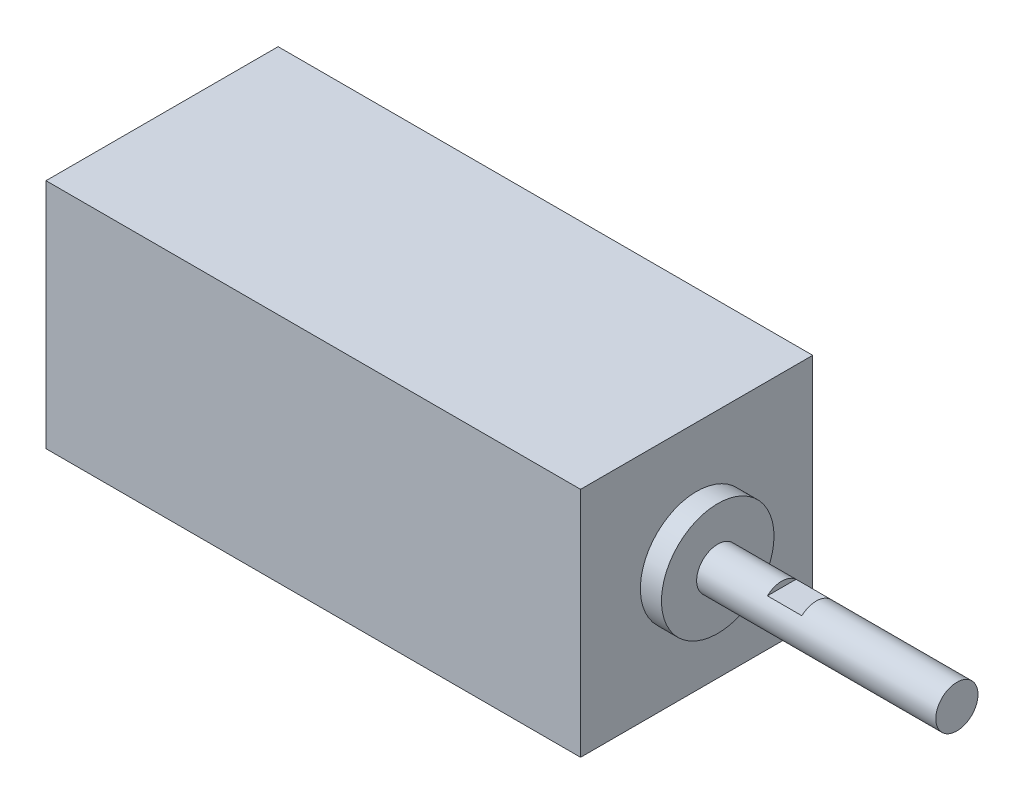
SolidWorks part; units mm, degrees
ref_plane "Front Plane" through (0, 0, 0) normal (0, 0, 1) x (1, 0, 0)
ref_plane "Top Plane" through (0, 0, 0) normal (0, 1, 0) x (1, 0, 0)
ref_plane "Right Plane" through (0, 0, 0) normal (1, 0, 0) x (0, 0, -1)
sketch "Sketch1" plane through (0, 0, 0) normal (1, 0, 0) x (0, 0, -1)
  line L1 (-16.5, -16.5) -> (16.5, -16.5)
  line L2 (-16.5, -16.5) -> (-16.5, 16.5)
  line L3 (-16.5, 16.5) -> (16.5, 16.5)
  line L4 (16.5, -16.5) -> (16.5, 16.5)
  line L5 (-16.5, -16.5) -> (16.5, 16.5) construction
  line L6 (-16.5, 16.5) -> (16.5, -16.5) construction
  point P0 (0, 0)
  dimension "D1" = 33
  dimension "D2" = 33
extrude "Boss-Extrude1" add sketch "Sketch1" along normal mid plane 76
sketch "Sketch2" plane through (38, 0, 0) normal (1, 0, 0) x (0, 0, -1)
  circle A0 centre (0, 0) radius 8
extrude "Boss-Extrude2" add sketch "Sketch2" along normal blind 3
sketch "Sketch3" plane through (41, 0, 0) normal (1, 0, 0) x (0, 0, -1)
  circle A0 centre (0, 0) radius 3
extrude "Boss-Extrude3" add sketch "Sketch3" along normal blind 34
sketch "Sketch4" plane through (0, 0, 0) normal (0, 0, 1) x (1, 0, 0)
  line L1 (50.1, 7.0386) -> (55, 7.0386)
  line L2 (50.1, 7.0386) -> (50.1, 2.2025)
  line L3 (50.1, 2.2025) -> (55, 2.2025)
  line L4 (55, 7.0386) -> (55, 2.2025)
  line L5 (50.1, 7.0386) -> (55, 2.2025) construction
  line L6 (50.1, 2.2025) -> (55, 7.0386) construction
  line L7 (75, -3) -> (75, 3) construction
  point P0 (52.55, 4.6206)
  dimension "D1" = 20
  dimension "D2" = 4.9
extrude "Cut-Extrude1" cut sketch "Sketch4" against normal mid plane 34
